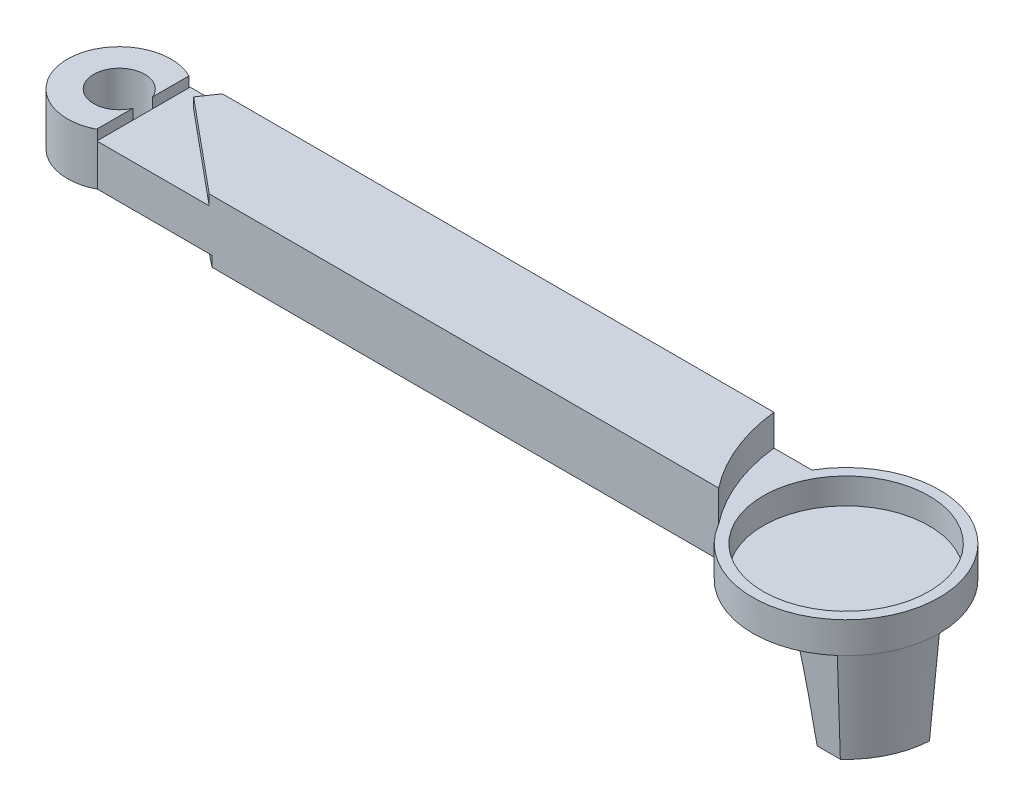
SolidWorks part; units mm, degrees
material "ABS"
ref_plane "Front Plane" through (0, 0, 0) normal (0, 0, 1) x (1, 0, 0)
ref_plane "Top Plane" through (0, 0, 0) normal (0, 1, 0) x (1, 0, 0)
ref_plane "Right Plane" through (0, 0, 0) normal (1, 0, 0) x (0, 0, -1)
sketch "Sketch2" plane through (0, 0, 0) normal (0, 1, 0) x (1, 0, 0)
  line L0 (0, 0) -> (60, 0)
  line L1 (0, 9) -> (60, 9)
  line L2 (0, 0) -> (0, 9)
  arc A1 (60, 9) -> (60, 0) centre (67.7942, 4.5) cw
  dimension "D1" = 9
  dimension "D2" = 60
  dimension "D4" = 9
  dimension "D3" = 60
extrude "Boss-Extrude1" add sketch "Sketch2" along normal blind 6
sketch "Sketch3" plane through (0, 6, 0) normal (0, 1, 0) x (1, 0, 0)
  circle A0 centre (67.7942, 4.5) radius 9
extrude "Cut-Extrude1" cut sketch "Sketch3" against normal blind 3
sketch "Sketch5" plane through (0, 6, 0) normal (0, 1, 0) x (1, 0, 0)
  line L0 (0, 0) -> (60, 0) construction
  line L1 (60, 9) -> (0, 9) construction
  arc A0 (60, 0) -> (56.3308, 9) centre (74.0459, 10.9743) cw
  arc A1 (60, 9) -> (60, 0) centre (67.7942, 4.5) ccw construction
  arc A2 (60, 0) -> (60, 9) centre (67.7942, 4.5) ccw construction
extrude "Cut-Extrude5" cut sketch "Sketch5" against normal blind 3 and the other way through all flip side to cut
sketch "Sketch6" plane through (0, 6, 0) normal (0, 1, 0) x (1, 0, 0)
  arc A0 (2.5668, 3.1489) -> (2.7043, 4.9581) centre (-2.2673, 4.4262) cw
  dimension "D1" = 5
extrude "Extrude-Thin3" add sketch "Sketch6" against normal blind 6 thin
sketch "Sketch7" plane through (0, 6, 0) normal (0, 1, 0) x (1, 0, 0)
  line L0 (0, 0) -> (0, 9)
  line L1 (0, 9) -> (10.8365, 0)
  line L2 (0.0584, 0) -> (60, 0) construction
  line L3 (0, 0) -> (10.8365, 0)
extrude "Cut-Extrude9" cut sketch "Sketch7" against normal blind 1
sketch "Sketch8" plane through (0, 6, 0) normal (0, 1, 0) x (1, 0, 0)
  line L0 (1.9829, 7.3531) -> (3.1178, 9)
  line L1 (10.8365, 0) -> (0, 9) construction
  line L2 (56.3308, 9) -> (0, 9) construction
  dimension "D1" = 2
extrude "Cut-Extrude10" cut sketch "Sketch8" against normal blind 1 and the other way through all
sketch "Sketch9" plane through (0, 0, 0) normal (0, -1, 0) x (-1, 0, 0)
  line L0 (-73.7208, -2.2732) -> (-69.7208, -2.2732)
  line L1 (-76.7942, 4.5) -> (-72.7942, 4.5)
  arc A0 (-73.7208, -2.2732) -> (-76.7942, 4.5) centre (-67.7942, 4.5) cw
  arc A1 (-60, 9) -> (-60, 0) centre (-67.7942, 4.5) ccw construction
  arc A2 (-69.7208, -2.2732) -> (-72.7942, 4.5) centre (-67.2331, 2.9395) cw
  dimension "D1" = 4
  dimension "D2" = 4
extrude "Boss-Extrude3" add sketch "Sketch9" along normal blind 9 draft 3
sketch "Sketch14" plane through (0, 3, 0) normal (0, 1, 0) x (1, 0, 0)
  circle A0 centre (67.7942, 4.5) radius 8
  arc A1 (76.7942, 4.5) -> (60, 9) centre (67.7942, 4.5) ccw construction
  arc A2 (60, 0) -> (60, 9) centre (67.7942, 4.5) ccw construction
  dimension "D1" = 1
extrude "Cut-Extrude13" cut sketch "Sketch14" against normal blind 2.5
sketch "Sketch16" plane through (0, 0, 0) normal (0, -1, 0) x (-1, 0, 0)
  line L0 (0, 8.8825) -> (-11.106, 0)
  line L1 (-0.0584, 0) -> (-60, 0) construction
extrude "Cut-Extrude15" cut sketch "Sketch16" against normal blind 1 and the other way through all contours L0
